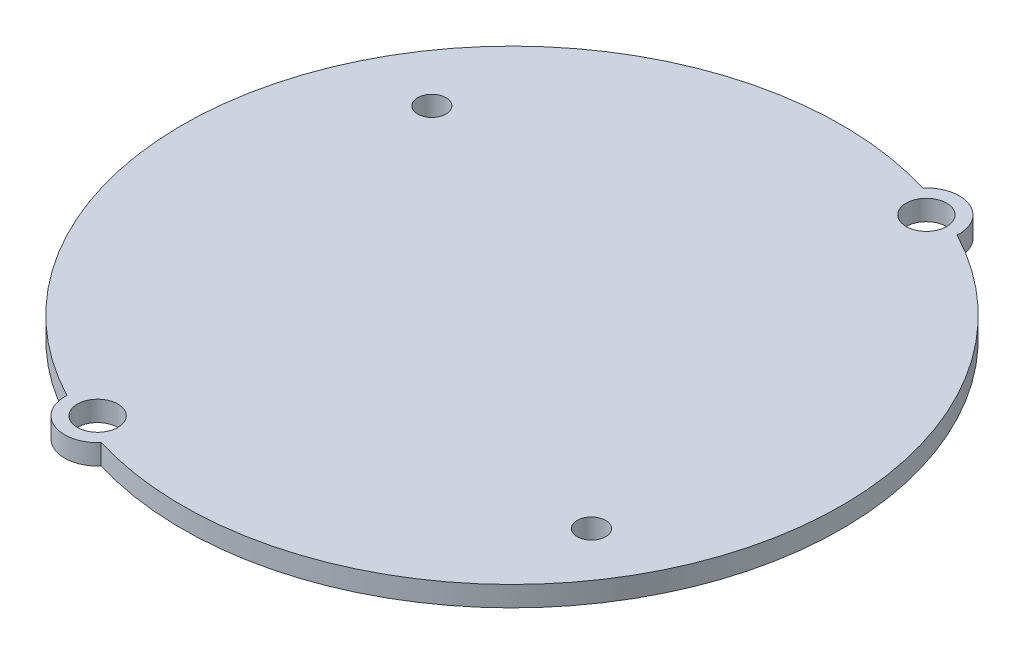
SolidWorks part; units mm, degrees
ref_plane "Front Plane" through (0, 0, 0) normal (0, 0, 1) x (1, 0, 0)
ref_plane "Top Plane" through (0, 0, 0) normal (0, 1, 0) x (1, 0, 0)
ref_plane "Right Plane" through (0, 0, 0) normal (1, 0, 0) x (0, 0, -1)
sketch "Sketch1" plane through (0, 0, 0) normal (0, 1, 0) x (1, 0, 0)
  line L0 (-0.3911, -32.498) -> (0.3911, 32.498) construction
  line L1 (32.5004, 0) -> (-32.5004, 0) construction
  arc A0 (9.3831, 31.116) -> (-15.0926, -28.783) centre (0, 0) ccw
  circle A1 centre (11.8499, 29) radius 2
  circle A2 centre (-11.8499, -29) radius 2
  arc A3 (15.0926, 28.783) -> (9.3831, 31.116) centre (11.8499, 29) ccw
  arc A4 (-15.0926, -28.783) -> (-9.3831, -31.116) centre (-11.8499, -29) ccw
  arc A6 (-9.3831, -31.116) -> (15.0926, 28.783) centre (0, 0) ccw
  point P6 (0, 0)
  point P9 (0, 0)
  dimension "D1" = 65
  dimension "D2" = 4
  dimension "D3" = 4
  dimension "D4" = 6.5
  dimension "D5" = 6.5
  dimension "D6" = 11.5
  dimension "D7" = 29
  dimension "D8" = 29
  dimension "D9" = 11.5
extrude "Boss-Extrude1" add sketch "Sketch1" along normal blind 2
sketch " PCB_layout_TV" plane through (0, 2, 0) normal (0, 1, 0) x (1, 0, 0)
  line L0 (-16.83, 11.0801) -> (-30.5533, 11.0801)
  line L1 (17.3381, -8.4426) -> (31.3846, -8.4426)
  line L2 (-16.83, 11.0801) -> (-16.83, -27.8029)
  line L3 (17.3381, -8.4426) -> (17.3381, 27.4893)
  circle A0 centre (0, 0) radius 32.5004
  dimension "D2" = 65.0007
  dimension "D1" = 14.0465
sketch "PCB_Layout_BV" plane through (0, 0, 0) normal (0, -1, 0) x (1, 0, 0)
  line L11 (-13.2307, 11.7284) -> (-30.31, 11.7284)
  line L12 (-13.2307, 24.6921) -> (-21.1318, 24.6921)
  line L13 (-13.2307, 11.7284) -> (-13.2307, 24.6921)
  line L14 (14.1696, -24.342) -> (21.5341, -24.342)
  line L15 (14.1696, -7.1585) -> (31.7018, -7.1585)
  line L16 (14.1696, -24.342) -> (14.1696, -7.1585)
  line L17 (8.9939, -8.5472) -> (8.9939, 8.4421)
  line L18 (-16.7432, 8.4421) -> (8.9939, 8.4421)
  line L19 (-16.7432, -8.5472) -> (-16.7432, 8.4421)
  line L20 (-16.7432, -8.5472) -> (8.9939, -8.5472)
  circle A3 centre (24.5007, 12.4235) radius 1.4
  circle A4 centre (-21.83, -13.9266) radius 1.4
  circle A5 centre (0, 0) radius 32.5
  dimension "D1" = 7.9011
sketch "Sketch6" plane through (0, 0, 0) normal (0, -1, 0) x (1, 0, 0)
  line L0 (-13.2307, 11.7284) -> (-30.31, 11.7284)
  line L1 (-13.2307, 24.6921) -> (-21.1318, 24.6921)
  line L2 (-13.2307, 11.7284) -> (-13.2307, 24.6921)
  line L3 (14.1696, -24.342) -> (21.5341, -24.342)
  line L4 (14.1696, -7.1585) -> (31.7018, -7.1585)
  line L5 (14.1696, -24.342) -> (14.1696, -7.1585)
  line L6 (8.9939, -8.5472) -> (8.9939, 8.4421)
  line L7 (-16.7432, 8.4421) -> (8.9939, 8.4421)
  line L8 (-16.7432, -8.5472) -> (-16.7432, 8.4421)
  line L9 (-16.7432, -8.5472) -> (8.9939, -8.5472)
  circle A0 centre (22.12, 14.29) radius 1.4
  circle A1 centre (-21.83, -13.9266) radius 1.4
  circle A2 centre (0, 0) radius 32.5
  dimension "D1" = 7.9011
  dimension "D2" = 22.12
  dimension "D3" = 14.29
extrude "Cut-Extrude1" cut sketch "Sketch6" against normal blind 10 contours A1 | A0
sketch "Sketch7" [suppressed] plane through (0, 2, 0) normal (0, 1, 0) x (1, 0, 0)
  line L0 (-0.3911, -32.498) -> (0.3911, 32.498) construction
  line L1 (32.5004, 0) -> (-32.5004, 0) construction
  circle A0 centre (0, 0) radius 32.5004 construction
  circle A1 centre (11.8499, 29) radius 2
  circle A2 centre (-11.8499, -29) radius 2
  circle A3 centre (11.8499, 29) radius 3.25
  circle A4 centre (-11.8499, -29) radius 3.25
  point P6 (0, 0)
  point P10 (0, 0)
  dimension "D1" = 4
  dimension "D2" = 4
  dimension "D3" = 6.5
  dimension "D4" = 6.5
  dimension "D5" = 11.5
  dimension "D6" = 29
  dimension "D7" = 29
  dimension "D8" = 11.5
